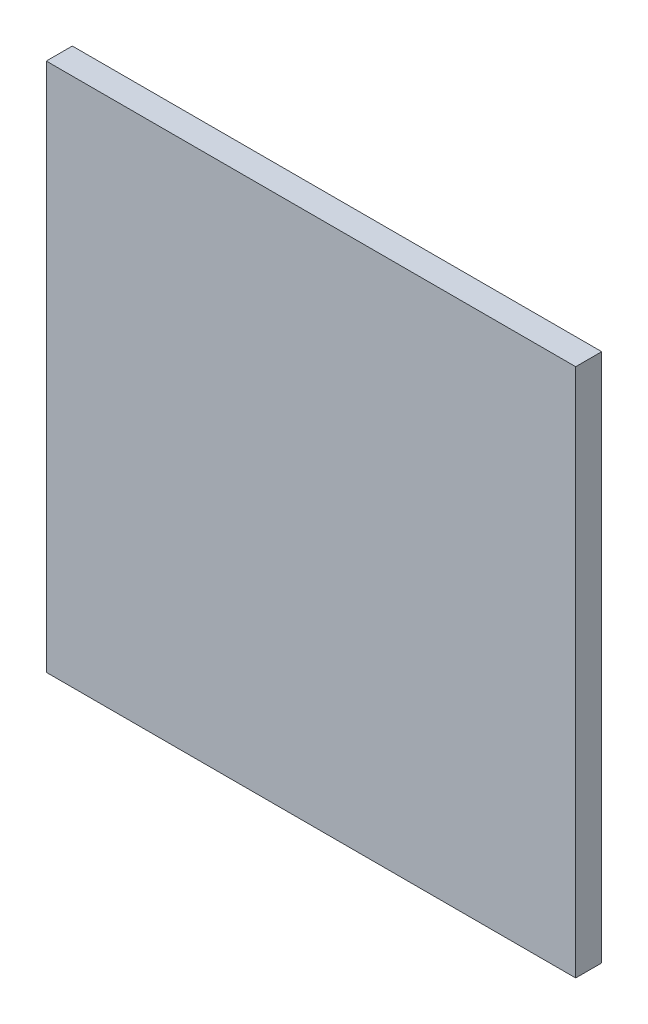
SolidWorks part; units mm, degrees
ref_plane "Front Plane" through (0, 0, 0) normal (0, 0, 1) x (1, 0, 0)
ref_plane "Top Plane" through (0, 0, 0) normal (0, 1, 0) x (1, 0, 0)
ref_plane "Right Plane" through (0, 0, 0) normal (1, 0, 0) x (0, 0, -1)
sketch "Sketch1" plane through (0, 0, 0) normal (0, 0, 1) x (1, 0, 0)
  line L1 (-152.5, -152.5) -> (152.5, -152.5)
  line L2 (-152.5, -152.5) -> (-152.5, 152.5)
  line L3 (-152.5, 152.5) -> (152.5, 152.5)
  line L4 (152.5, -152.5) -> (152.5, 152.5)
  line L5 (-152.5, -152.5) -> (152.5, 152.5) construction
  line L6 (-152.5, 152.5) -> (152.5, -152.5) construction
  point P0 (0, 0)
  dimension "D1" = 305
  dimension "D2" = 305
extrude "Boss-Extrude1" add sketch "Sketch1" along normal blind 15
sketch "Sketch2" plane through (0, 0, 0) normal (0, 0, -1) x (-1, 0, 0)
  line L0 (115.48, 106.0834) -> (139.343, 106.0834)
  line L1 (139.343, 106.0834) -> (139.343, 131.8037)
  line L8 (135.9292, 134.0654) -> (135.9292, 135.6745)
  line L9 (135.9292, 135.6745) -> (136.868, 136.6133)
  line L10 (139.343, 139.0882) -> (139.343, 137.3814)
  line L11 (139.343, 137.3814) -> (138.2797, 136.3486)
  line L12 (139.343, 134.0654) -> (137.6857, 135.7715)
  line L13 (115.48, 106.0834) -> (115.48, 108.0834)
  line L14 (115.48, 108.0834) -> (137.343, 108.0834)
  line L15 (137.343, 108.0834) -> (137.343, 131.8037)
  line L16 (137.343, 131.8037) -> (139.343, 131.8037)
  line L17 (135.9292, 137.5798) -> (135.9292, 138.7684)
  line L18 (135.9292, 138.7684) -> (137.4537, 137.199)
  line L19 (139.343, 135.254) -> (139.343, 134.0654)
  line L20 (110.817, 103.0023) -> (112.7578, 104.9431)
  line L21 (112.7578, 104.9431) -> (115.0245, 102.6764)
  line L22 (115.0245, 102.6764) -> (115.0245, 104.2263)
  line L23 (115.0245, 104.2263) -> (110.9457, 107.8767)
  line L24 (110.9457, 107.8767) -> (110.9457, 106.7263)
  line L25 (110.9457, 106.7263) -> (112.1165, 105.6784)
  line L26 (112.1165, 105.6784) -> (110.817, 104.2263)
  line L27 (110.817, 104.2263) -> (110.817, 103.0023)
  line L28 (138.2797, 136.3486) -> (139.343, 135.254)
  line L29 (136.868, 136.6133) -> (135.9292, 137.5798)
  line L30 (137.4537, 137.199) -> (139.343, 139.0882)
  line L31 (137.6857, 135.7715) -> (135.9292, 134.0654)
extrude "Boss-Extrude2" [suppressed] add sketch "Sketch2" along normal blind 2
sketch "Sketch4" [suppressed] plane through (0, 0, -2) normal (0, 0, -1) x (-1, 0, 0)
  line L0 (137.343, 108.0834) -> (137.343, 106.0834)
  line L1 (115.48, 106.0834) -> (139.343, 106.0834) construction
  line L2 (137.343, 106.0834) -> (137.6315, 106.0834)
  line L3 (139.343, 106.0834) -> (139.343, 108.0834)
  line L4 (139.343, 106.0834) -> (139.343, 131.8037) construction
  line L5 (139.343, 108.0834) -> (139.0972, 108.0834)
  line L6 (137.6315, 106.0834) -> (137.6315, 107.7023)
  line L7 (137.6315, 107.7023) -> (139.343, 106.0834)
  line L8 (139.343, 106.0834) -> (139.343, 108.0834)
  line L9 (137.6315, 108.0834) -> (139.0972, 106.6177)
  line L10 (139.0972, 106.6177) -> (139.0972, 108.0834)
  line L11 (137.6315, 108.0834) -> (137.343, 108.0834)
  line M2 (115.48, 106.0834) -> (139.343, 106.0834)
  line M3 (139.343, 106.0834) -> (139.343, 131.8037)
extrude "Boss-Extrude3" [suppressed] add sketch "Sketch4" along normal blind 20 contours L9 L11 L0 L6 L7 L5 L10 M2 M3
equation "\"length\"= 300mm'length base"
equation "\"breadth\"= 300mm'breadth base"
equation "\"heght\"= 15'Height base"
equation "\"D1@Boss-Extrude1\"=\"heght\""
